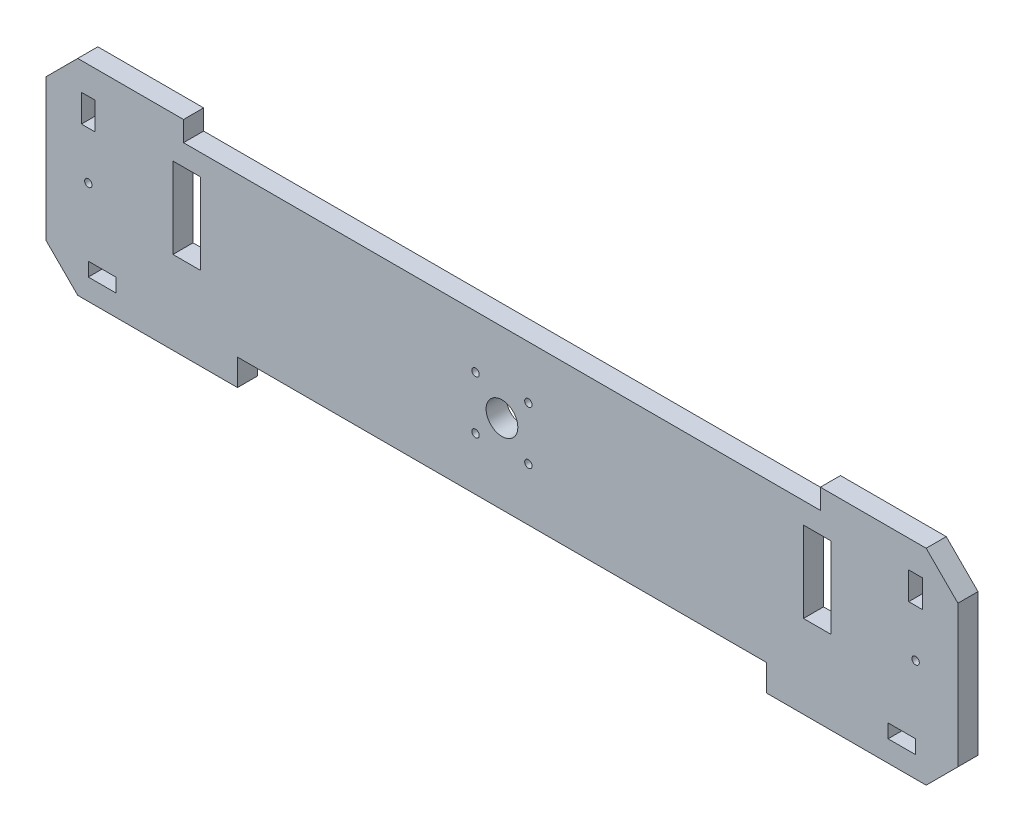
SolidWorks part; units mm, degrees
ref_plane "Alzado" through (0, 0, 0) normal (0, 0, 1) x (1, 0, 0)
ref_plane "Planta" through (0, 0, 0) normal (0, 1, 0) x (1, 0, 0)
ref_plane "Vista lateral" through (0, 0, 0) normal (1, 0, 0) x (0, 0, -1)
sketch "Croquis1" plane through (0, 0, 0) normal (0, 0, 1) x (1, 0, 0)
  line L0 (-301, 194) -> (-301, 175)
  line L1 (-250, 25) -> (250, 25)
  line L2 (250, 25) -> (250, 0)
  line L3 (250, 0) -> (401, 0)
  line L4 (401, 0) -> (431, 30)
  line L5 (431, 30) -> (431, 164)
  line L6 (431, 164) -> (401, 194)
  line L7 (401, 194) -> (301, 194)
  line L8 (301, 194) -> (301, 175)
  line L9 (301, 175) -> (-301, 175)
  line L10 (-401, 194) -> (-301, 194)
  line L11 (-431, 164) -> (-401, 194)
  line L12 (-431, 30) -> (-431, 164)
  line L13 (0, 0) -> (0, 25) construction
  line L14 (0, 25) -> (0, 175) construction
  line L15 (-401, 0) -> (-431, 30)
  line L16 (-250, 0) -> (-401, 0)
  line L17 (-250, 25) -> (-250, 0)
  line L18 (-391, 0) -> (-391, 97) construction
  line L19 (-311, 155) -> (-285, 155)
  line L20 (-311, 155) -> (-311, 78.5)
  line L21 (-311, 78.5) -> (-285, 78.5)
  line L22 (-285, 155) -> (-285, 78.5)
  line L23 (-311, 155) -> (-285, 78.5) construction
  line L24 (-311, 78.5) -> (-285, 155) construction
  line L25 (-391, 97) -> (-391, 194) construction
  line L26 (311, 78.5) -> (285, 78.5)
  line L27 (311, 155) -> (311, 78.5)
  line L28 (311, 155) -> (285, 155)
  line L29 (285, 155) -> (285, 78.5)
  line L31 (25, 75) -> (-25, 75) construction
  line L32 (25, 75) -> (25, 125) construction
  line L33 (25, 125) -> (-25, 125) construction
  line L34 (-25, 75) -> (-25, 125) construction
  line L35 (25, 75) -> (-25, 125) construction
  line L36 (25, 125) -> (-25, 75) construction
  line L41 (391, 33) -> (391, 20)
  line L43 (-365, 33) -> (-391, 33)
  line L44 (-365, 33) -> (-365, 20)
  line L45 (-365, 20) -> (-391, 20)
  line L46 (-391, 33) -> (-391, 20)
  line L47 (-365, 33) -> (-391, 20) construction
  line L48 (-365, 20) -> (-391, 33) construction
  line L49 (365, 20) -> (391, 20)
  line L50 (365, 33) -> (365, 20)
  line L51 (365, 33) -> (391, 33)
  line L52 (397.5, 168) -> (397.5, 142)
  line L53 (-397.5, 168) -> (-384.5, 168)
  line L54 (-397.5, 168) -> (-397.5, 142)
  line L55 (-397.5, 142) -> (-384.5, 142)
  line L56 (-384.5, 168) -> (-384.5, 142)
  line L57 (-397.5, 168) -> (-384.5, 142) construction
  line L58 (-397.5, 142) -> (-384.5, 168) construction
  line L59 (397.5, 168) -> (384.5, 168)
  line L60 (384.5, 168) -> (384.5, 142)
  line L61 (397.5, 142) -> (384.5, 142)
  circle A0 centre (-391, 97) radius 3.5
  circle A1 centre (391, 97) radius 3.5
  circle A2 centre (0, 100) radius 15
  circle A3 centre (-25, 125) radius 3.5
  circle A4 centre (25, 125) radius 3.5
  circle A5 centre (25, 75) radius 3.5
  circle A6 centre (-25, 75) radius 3.5
  point P20 (-298, 116.75)
  point P57 (-378, 26.5)
  point P66 (-391, 155)
  dimension "D14" = 40
  dimension "D15" = 7
  dimension "D16" = 30
  dimension "D17" = 7
  dimension "D1" = 150
  dimension "D2" = 301
  dimension "D3" = 100
  dimension "D4" = 19
  dimension "D5" = 135
  dimension "D6" = 30
  dimension "D7" = 25
  dimension "D8" = 250
  dimension "D9" = 30
  dimension "D10" = 76.5
  dimension "D11" = 26
  dimension "D12" = 10
  dimension "D13" = 20
  dimension "D18" = 50
  dimension "D19" = 50
  dimension "D31" = 26
  dimension "D32" = 13
  dimension "D33" = 20
  dimension "D34" = 40
  dimension "D35" = 26
  dimension "D36" = 194
  dimension "D37" = 862
extrude "Saliente-Extruir1" add sketch "Croquis1" along normal blind 19
